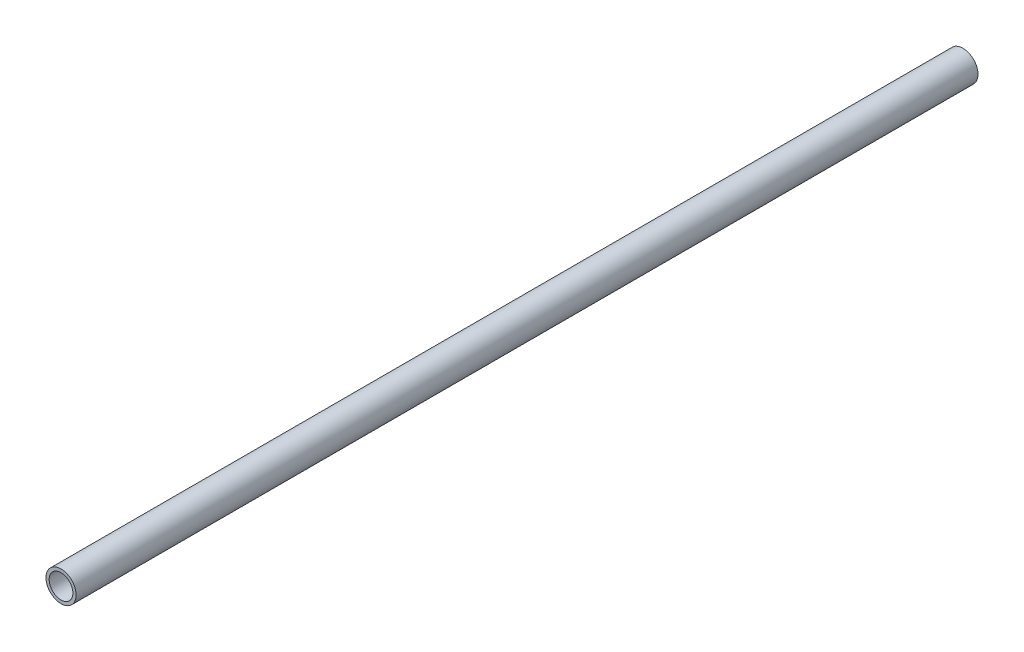
SolidWorks part; units mm, degrees
material "Thornel Mat VMA"
ref_plane "Płaszczyzna XY" through (0, 0, 0) normal (0, 0, 1) x (1, 0, 0)
ref_plane "Płaszczyzna XZ" through (0, 0, 0) normal (0, 1, 0) x (1, 0, 0)
ref_plane "Płaszczyzna YZ" through (0, 0, 0) normal (1, 0, 0) x (0, 0, -1)
sketch "Sketch1" plane through (0, 0, 0) normal (0, 0, 1) x (1, 0, 0)
  circle A0 centre (0, 0) radius 6.35
  circle A1 centre (0, 0) radius 5
  dimension "D1" = 12.7
  dimension "D2" = 10
extrude "Boss-Extrude1" add sketch "Sketch1" along normal blind 380.28
